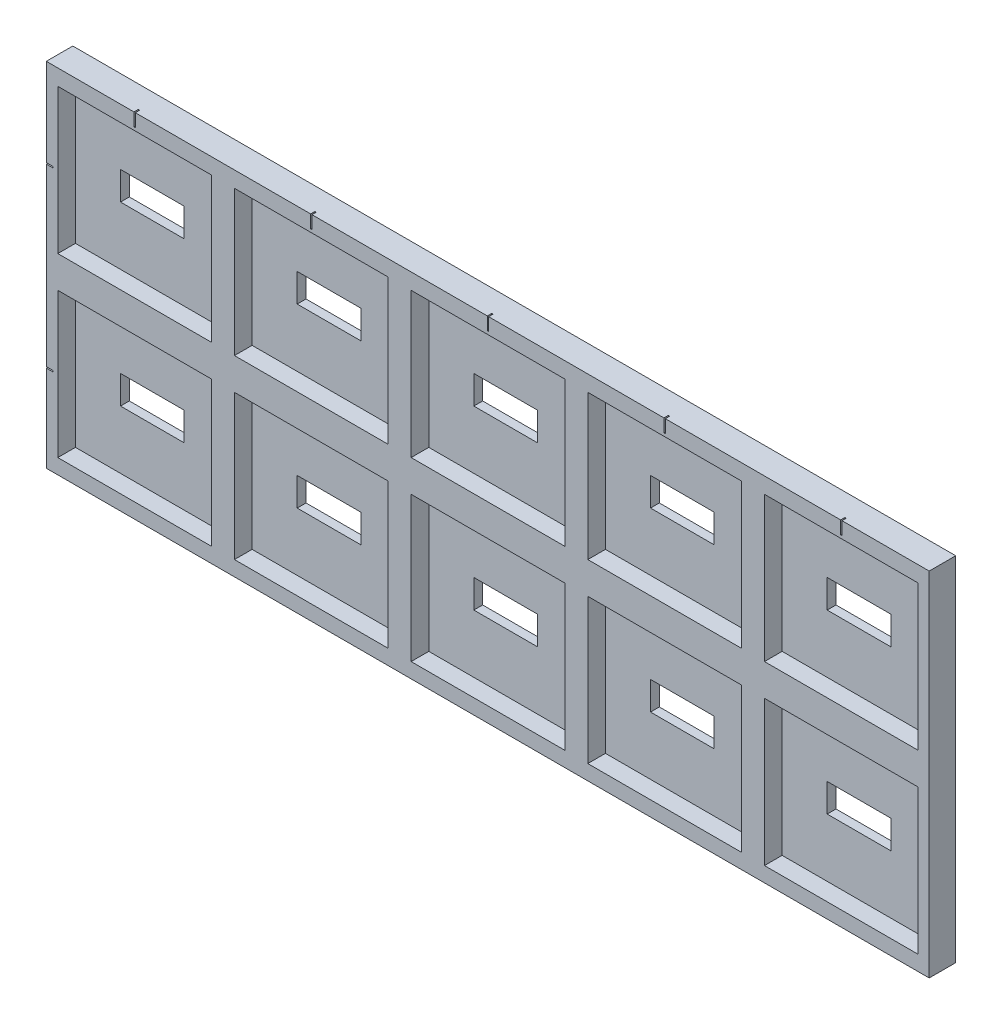
SolidWorks part; units mm, degrees
material "Plastique personnalisé"
ref_plane "Plan de face" through (0, 0, 0) normal (0, 0, 1) x (1, 0, 0)
ref_plane "Plan de dessus" through (0, 0, 0) normal (0, 1, 0) x (1, 0, 0)
ref_plane "Plan de droite" through (0, 0, 0) normal (1, 0, 0) x (0, 0, -1)
sketch "alcove" plane through (0, 0, 0) normal (0, 0, 1) x (1, 0, 0)
  line L0 (11.3, -8.2) -> (28.7, -8.2)
  line L1 (-8.7, -8.2) -> (8.7, -8.2)
  line L2 (-8.7, -8.2) -> (-8.7, 8.2)
  line L3 (-8.7, 8.2) -> (8.7, 8.2)
  line L4 (8.7, -8.2) -> (8.7, 8.2)
  line L5 (-8.7, -8.2) -> (8.7, 8.2) construction
  line L6 (-8.7, 8.2) -> (8.7, -8.2) construction
  line L7 (11.3, -8.2) -> (11.3, 8.2)
  line L8 (11.3, 8.2) -> (28.7, 8.2)
  line L9 (28.7, -8.2) -> (28.7, 8.2)
  line L10 (11.3, -8.2) -> (28.7, 8.2) construction
  line L11 (11.3, 8.2) -> (28.7, -8.2) construction
  line L12 (31.3, -8.2) -> (48.7, -8.2)
  line L13 (31.3, -8.2) -> (31.3, 8.2)
  line L14 (31.3, 8.2) -> (48.7, 8.2)
  line L15 (48.7, -8.2) -> (48.7, 8.2)
  line L16 (31.3, -8.2) -> (48.7, 8.2) construction
  line L17 (31.3, 8.2) -> (48.7, -8.2) construction
  line L18 (51.3, -8.2) -> (68.7, -8.2)
  line L19 (51.3, -8.2) -> (51.3, 8.2)
  line L20 (51.3, 8.2) -> (68.7, 8.2)
  line L21 (68.7, -8.2) -> (68.7, 8.2)
  line L22 (51.3, -8.2) -> (68.7, 8.2) construction
  line L23 (51.3, 8.2) -> (68.7, -8.2) construction
  line L24 (71.3, -8.2) -> (88.7, -8.2)
  line L25 (71.3, -8.2) -> (71.3, 8.2)
  line L26 (71.3, 8.2) -> (88.7, 8.2)
  line L27 (88.7, -8.2) -> (88.7, 8.2)
  line L28 (71.3, -8.2) -> (88.7, 8.2) construction
  line L29 (71.3, 8.2) -> (88.7, -8.2) construction
  line L30 (11.3, -28.2) -> (28.7, -28.2)
  line L31 (11.3, -28.2) -> (11.3, -11.8)
  line L32 (11.3, -11.8) -> (28.7, -11.8)
  line L33 (28.7, -28.2) -> (28.7, -11.8)
  line L34 (11.3, -28.2) -> (28.7, -11.8) construction
  line L35 (11.3, -11.8) -> (28.7, -28.2) construction
  line L36 (31.3, -28.2) -> (48.7, -28.2)
  line L37 (31.3, -28.2) -> (31.3, -11.8)
  line L38 (31.3, -11.8) -> (48.7, -11.8)
  line L39 (48.7, -28.2) -> (48.7, -11.8)
  line L40 (31.3, -28.2) -> (48.7, -11.8) construction
  line L41 (31.3, -11.8) -> (48.7, -28.2) construction
  line L42 (51.3, -28.2) -> (68.7, -28.2)
  line L43 (51.3, -28.2) -> (51.3, -11.8)
  line L44 (51.3, -11.8) -> (68.7, -11.8)
  line L45 (68.7, -28.2) -> (68.7, -11.8)
  line L46 (51.3, -28.2) -> (68.7, -11.8) construction
  line L47 (51.3, -11.8) -> (68.7, -28.2) construction
  line L48 (71.3, -28.2) -> (88.7, -28.2)
  line L49 (71.3, -28.2) -> (71.3, -11.8)
  line L50 (71.3, -11.8) -> (88.7, -11.8)
  line L51 (88.7, -28.2) -> (88.7, -11.8)
  line L52 (71.3, -28.2) -> (88.7, -11.8) construction
  line L53 (71.3, -11.8) -> (88.7, -28.2) construction
  line L54 (-8.7, -28.2) -> (8.7, -28.2)
  line L55 (-8.7, -28.2) -> (-8.7, -11.8)
  line L56 (-8.7, -11.8) -> (8.7, -11.8)
  line L57 (8.7, -28.2) -> (8.7, -11.8)
  line L58 (-8.7, -28.2) -> (8.7, -11.8) construction
  line L59 (-8.7, -11.8) -> (8.7, -28.2) construction
  point P0 (0, 0)
  point P9 (20, 0)
  point P14 (40, 0)
  point P19 (60, 0)
  point P24 (80, 0)
  point P29 (20, -20)
  point P34 (40, -20)
  point P39 (60, -20)
  point P44 (80, -20)
  point P49 (0, -20)
  dimension "D1" = 17.4
  dimension "D2" = 16.4
  dimension "D3" = 5
  dimension "D4" = 2
sketch "pinspace" plane through (0, 0, 0) normal (0, 0, 1) x (1, 0, 0)
  line L0 (16.4, -1.6) -> (23.6, -1.6)
  line L1 (-3.6, -1.6) -> (3.6, -1.6)
  line L2 (-3.6, -1.6) -> (-3.6, 1.6)
  line L3 (-3.6, 1.6) -> (3.6, 1.6)
  line L4 (3.6, -1.6) -> (3.6, 1.6)
  line L5 (-3.6, -1.6) -> (3.6, 1.6) construction
  line L6 (-3.6, 1.6) -> (3.6, -1.6) construction
  line L7 (16.4, -1.6) -> (16.4, 1.6)
  line L8 (16.4, 1.6) -> (23.6, 1.6)
  line L9 (23.6, -1.6) -> (23.6, 1.6)
  line L10 (16.4, -1.6) -> (23.6, 1.6) construction
  line L11 (16.4, 1.6) -> (23.6, -1.6) construction
  line L12 (36.4, -1.6) -> (43.6, -1.6)
  line L13 (36.4, -1.6) -> (36.4, 1.6)
  line L14 (36.4, 1.6) -> (43.6, 1.6)
  line L15 (43.6, -1.6) -> (43.6, 1.6)
  line L16 (36.4, -1.6) -> (43.6, 1.6) construction
  line L17 (36.4, 1.6) -> (43.6, -1.6) construction
  line L18 (56.4, -1.6) -> (63.6, -1.6)
  line L19 (56.4, -1.6) -> (56.4, 1.6)
  line L20 (56.4, 1.6) -> (63.6, 1.6)
  line L21 (63.6, -1.6) -> (63.6, 1.6)
  line L22 (56.4, -1.6) -> (63.6, 1.6) construction
  line L23 (56.4, 1.6) -> (63.6, -1.6) construction
  line L24 (76.4, -1.6) -> (83.6, -1.6)
  line L25 (76.4, -1.6) -> (76.4, 1.6)
  line L26 (76.4, 1.6) -> (83.6, 1.6)
  line L27 (83.6, -1.6) -> (83.6, 1.6)
  line L28 (76.4, -1.6) -> (83.6, 1.6) construction
  line L29 (76.4, 1.6) -> (83.6, -1.6) construction
  line L30 (16.4, -21.6) -> (23.6, -21.6)
  line L31 (16.4, -21.6) -> (16.4, -18.4)
  line L32 (16.4, -18.4) -> (23.6, -18.4)
  line L33 (23.6, -21.6) -> (23.6, -18.4)
  line L34 (16.4, -21.6) -> (23.6, -18.4) construction
  line L35 (16.4, -18.4) -> (23.6, -21.6) construction
  line L36 (36.4, -21.6) -> (43.6, -21.6)
  line L37 (36.4, -21.6) -> (36.4, -18.4)
  line L38 (36.4, -18.4) -> (43.6, -18.4)
  line L39 (43.6, -21.6) -> (43.6, -18.4)
  line L40 (36.4, -21.6) -> (43.6, -18.4) construction
  line L41 (36.4, -18.4) -> (43.6, -21.6) construction
  line L42 (56.4, -21.6) -> (63.6, -21.6)
  line L43 (56.4, -21.6) -> (56.4, -18.4)
  line L44 (56.4, -18.4) -> (63.6, -18.4)
  line L45 (63.6, -21.6) -> (63.6, -18.4)
  line L46 (56.4, -21.6) -> (63.6, -18.4) construction
  line L47 (56.4, -18.4) -> (63.6, -21.6) construction
  line L48 (76.4, -21.6) -> (83.6, -21.6)
  line L49 (76.4, -21.6) -> (76.4, -18.4)
  line L50 (76.4, -18.4) -> (83.6, -18.4)
  line L51 (83.6, -21.6) -> (83.6, -18.4)
  line L52 (76.4, -21.6) -> (83.6, -18.4) construction
  line L53 (76.4, -18.4) -> (83.6, -21.6) construction
  line L54 (-3.6, -21.6) -> (3.6, -21.6)
  line L55 (-3.6, -21.6) -> (-3.6, -18.4)
  line L56 (-3.6, -18.4) -> (3.6, -18.4)
  line L57 (3.6, -21.6) -> (3.6, -18.4)
  line L58 (-3.6, -21.6) -> (3.6, -18.4) construction
  line L59 (-3.6, -18.4) -> (3.6, -21.6) construction
  point P0 (0, 0)
  point P9 (20, 0)
  point P14 (40, 0)
  point P19 (60, 0)
  point P24 (80, 0)
  point P29 (20, -20)
  point P34 (40, -20)
  point P39 (60, -20)
  point P44 (80, -20)
  point P49 (0, -20)
  dimension "D1" = 7.2
  dimension "D2" = 3.2
  dimension "D3" = 5
  dimension "D4" = 2
sketch "table" plane through (0, 0, 0) normal (0, 0, 1) x (1, 0, 0)
  line L0 (-8.6114, 8.2803) -> (88.5603, -28.1782) construction
  line L1 (0, 0) -> (0, 10) construction
  line L6 (0, 10) -> (-10, 10) construction
  line L7 (89.9489, -29.8979) -> (-10, -29.8979)
  line L8 (-8.7, 8.2) -> (8.7, -8.2) construction
  line L9 (0, 0) -> (-10, 0) construction
  line L10 (89.9489, -29.8979) -> (89.9489, 10)
  line L11 (89.9489, 10) -> (-10, 10)
  line L12 (-10, -29.8979) -> (-10, 10)
  line L13 (89.9489, -29.8979) -> (-10, 10) construction
  line L14 (89.9489, 10) -> (-10, -29.8979) construction
  line L15 (0, 10) -> (0, 12.5699) construction
  line L16 (0, 12.5699) -> (-10, 12.5699) construction
  line L17 (-10, 10) -> (-15.4651, 10) construction
  point P2 (39.9745, -9.9489)
  point P3 (39.9745, -9.9489)
  dimension "D1" = 10
  dimension "D2" = 10
  dimension "D3" = 99.9489
  dimension "D4" = 10
extrude "Boss.-Extru.1" add sketch "table" against normal blind 3
extrude "Enlèv. mat.-Extru.1" cut sketch "pinspace" against normal through all both and the other way through all
extrude "Enlèv. mat.-Extru.2" cut sketch "alcove" against normal blind 2
sketch "Esquisse4" plane through (0, 0, 0) normal (0, 0, 1) x (1, 0, 0)
  line L0 (0, 8.2) -> (0, 10) construction
  line L1 (8.7, 8.2) -> (-8.7, 8.2) construction
  line L2 (89.9489, 10) -> (-10, 10) construction
  line L3 (19.9235, 8.5402) -> (20.0765, 10.1707) construction
  line L4 (-0.0765, 8.5402) -> (0.0765, 8.5402)
  line L5 (-0.0765, 8.5402) -> (-0.0765, 10.1707)
  line L6 (-0.0765, 10.1707) -> (0.0765, 10.1707)
  line L7 (0.0765, 8.5402) -> (0.0765, 10.1707)
  line L8 (-0.0765, 8.5402) -> (0.0765, 10.1707) construction
  line L9 (-0.0765, 10.1707) -> (0.0765, 8.5402) construction
  line L10 (19.9235, 10.1707) -> (20.0765, 8.5402) construction
  line L11 (19.9235, 8.5402) -> (19.9235, 10.1707)
  line L12 (19.9235, 8.5402) -> (20.0765, 8.5402)
  line L13 (20.0765, 8.5402) -> (20.0765, 10.1707)
  line L14 (19.9235, 10.1707) -> (20.0765, 10.1707)
  line L15 (39.9235, 8.5402) -> (40.0765, 10.1707) construction
  line L16 (39.9235, 10.1707) -> (40.0765, 8.5402) construction
  line L17 (39.9235, 8.5402) -> (39.9235, 10.1707)
  line L18 (39.9235, 8.5402) -> (40.0765, 8.5402)
  line L19 (40.0765, 8.5402) -> (40.0765, 10.1707)
  line L20 (39.9235, 10.1707) -> (40.0765, 10.1707)
  line L21 (59.9235, 8.5402) -> (60.0765, 10.1707) construction
  line L22 (59.9235, 10.1707) -> (60.0765, 8.5402) construction
  line L23 (59.9235, 8.5402) -> (59.9235, 10.1707)
  line L24 (59.9235, 8.5402) -> (60.0765, 8.5402)
  line L25 (60.0765, 8.5402) -> (60.0765, 10.1707)
  line L26 (59.9235, 10.1707) -> (60.0765, 10.1707)
  line L27 (79.9235, 8.5402) -> (80.0765, 10.1707) construction
  line L28 (79.9235, 10.1707) -> (80.0765, 8.5402) construction
  line L29 (79.9235, 8.5402) -> (79.9235, 10.1707)
  line L30 (79.9235, 8.5402) -> (80.0765, 8.5402)
  line L31 (80.0765, 8.5402) -> (80.0765, 10.1707)
  line L32 (79.9235, 10.1707) -> (80.0765, 10.1707)
  line L33 (-8.7, 0) -> (-10, 0) construction
  line L34 (-8.7, 8.2) -> (-8.7, -8.2) construction
  line L35 (-10, 10) -> (-10, -29.8979) construction
  line L36 (-9.263, -20.0735) -> (-10.1078, -19.9265) construction
  line L37 (-9.263, -0.0735) -> (-10.1078, -0.0735)
  line L38 (-9.263, -0.0735) -> (-9.263, 0.0735)
  line L39 (-9.263, 0.0735) -> (-10.1078, 0.0735)
  line L40 (-10.1078, -0.0735) -> (-10.1078, 0.0735)
  line L41 (-9.263, -0.0735) -> (-10.1078, 0.0735) construction
  line L42 (-9.263, 0.0735) -> (-10.1078, -0.0735) construction
  line L43 (-9.263, -19.9265) -> (-10.1078, -20.0735) construction
  line L44 (-9.263, -20.0735) -> (-9.263, -19.9265)
  line L45 (-9.263, -20.0735) -> (-10.1078, -20.0735)
  line L46 (-10.1078, -20.0735) -> (-10.1078, -19.9265)
  line L47 (-9.263, -19.9265) -> (-10.1078, -19.9265)
  point P7 (0, 9.3555)
  point P14 (20, 9.3555)
  point P19 (40, 9.3555)
  point P24 (60, 9.3555)
  point P29 (80, 9.3555)
  point P38 (-9.6854, 0)
  point P44 (-9.6854, -20)
  dimension "D1" = 5
  dimension "D2" = 2
extrude "Enlèv. mat.-Extru.3" cut sketch "Esquisse4" against normal blind 0.5
